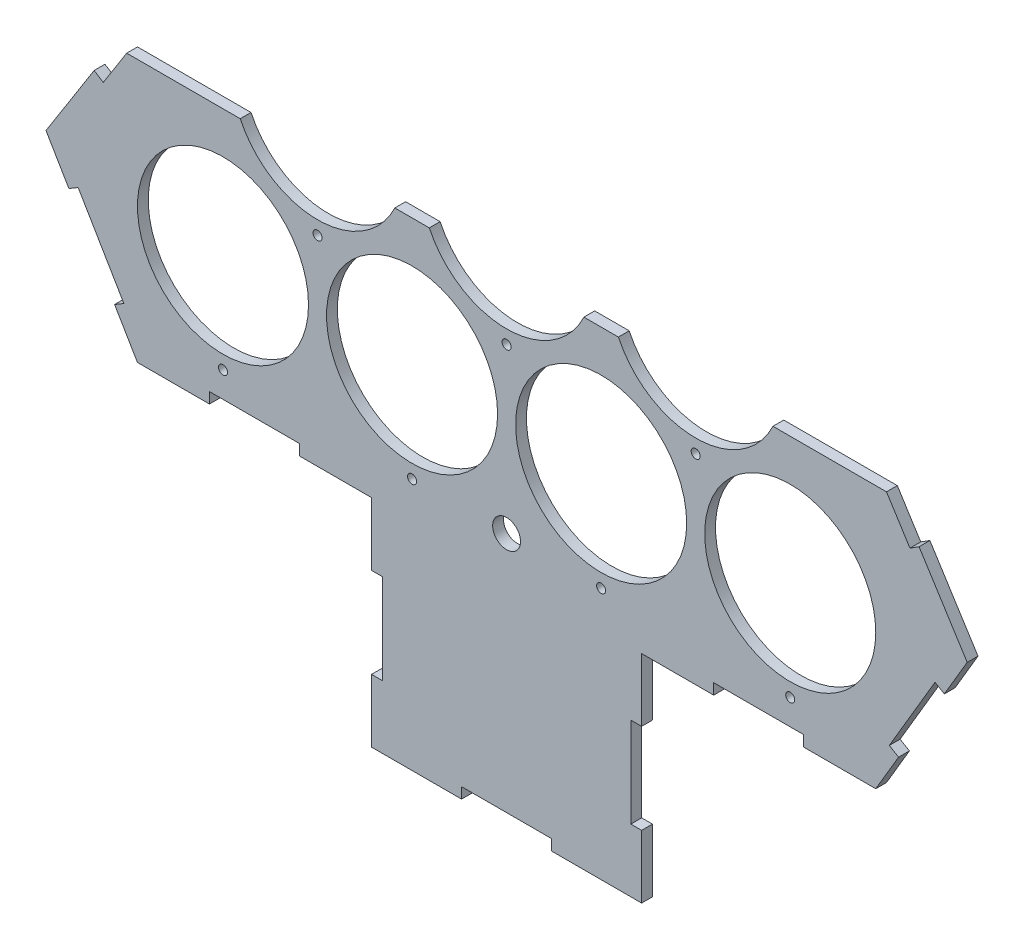
SolidWorks part; units mm, degrees
ref_plane "Plan de face" through (0, 0, 0) normal (0, 0, 1) x (1, 0, 0)
ref_plane "Plan de dessus" through (0, 0, 0) normal (0, 1, 0) x (1, 0, 0)
ref_plane "Plan de droite" through (0, 0, 0) normal (1, 0, 0) x (0, 0, -1)
sketch "Esquisse1" plane through (0, 0, 0) normal (0, 0, 1) x (1, 0, 0)
  line L0 (0, 0) -> (-371.1464, 0) construction
  line L1 (0, 0) -> (478.5179, 0) construction
  line L2 (0, 0) -> (0, 90.9327) construction
  line L3 (0, 90.9327) -> (-157.5, 90.9327) construction
  line L4 (0, 90.9327) -> (157.5, 90.9327) construction
  line L5 (0, 90.9327) -> (0, 181.8653) construction
  line L6 (0, 181.8653) -> (-52.5, 181.8653) construction
  line L7 (0, 181.8653) -> (52.5, 181.8653) construction
  line L8 (0, 181.8653) -> (0, 363.4062) construction
  line L12 (-255.7759, 10.9597) -> (-205, -75.1903)
  line L13 (205, -75.1903) -> (255.7759, 10.9597)
  line L14 (-50, 336.3537) -> (50, 336.3537)
  line L15 (-205, -75.1903) -> (205, -75.1903)
  line L16 (255.7759, 10.9597) -> (50, 336.3537)
  line L17 (-50, 336.3537) -> (-255.7759, 10.9597)
  line L18 (-50, 336.3537) -> (-50, -75.1903) construction
  line L19 (50, 336.3537) -> (50, -75.1903) construction
  circle A0 centre (-157.5, 0) radius 47.5
  circle A1 centre (-52.5, 0) radius 47.5
  circle A2 centre (52.5, 0) radius 47.5
  circle A3 centre (157.5, 0) radius 47.5
  circle A4 centre (-105, 90.9327) radius 47.5
  circle A5 centre (0, 90.9327) radius 47.5
  circle A6 centre (105, 90.9327) radius 47.5
  circle A7 centre (-52.5, 181.8653) radius 47.5
  circle A8 centre (52.5, 181.8653) radius 47.5
  circle A9 centre (0, 272.798) radius 47.5
  dimension "D1" = 95
  dimension "D2" = 95
  dimension "D3" = 95
  dimension "D4" = 95
  dimension "D5" = 105
  dimension "D6" = 52.5
  dimension "D7" = 52.5
  dimension "D8" = 105
  dimension "D9" = 95
  dimension "D10" = 95
  dimension "D11" = 95
  dimension "D12" = 105
  dimension "D13" = 105
  dimension "D14" = 105
  dimension "D15" = 95
  dimension "D16" = 95
  dimension "D17" = 105
  dimension "D18" = 52.5
  dimension "D19" = 52.5
  dimension "D20" = 95
  dimension "D21" = 105
  dimension "D27" = 205
  dimension "D22" = 385
  dimension "D23" = 385
  dimension "D24" = 410
  dimension "D25" = 32.309
  dimension "D26" = 32.309
  dimension "D28" = 100
  dimension "D30" = 100
  dimension "D31" = 100
extrude "Boss.-Extru.1" add sketch "Esquisse1" along normal blind 6
sketch "Esquisse9" plane through (0, 0, 6) normal (0, 0, 1) x (1, 0, 0)
  line L0 (-205, -75.1903) -> (205, -75.1903) construction
  line L1 (-75, -75.1903) -> (75, -75.1903)
  line L2 (-75, -75.1903) -> (-75, -195.1903)
  line L3 (-75, -195.1903) -> (75, -195.1903)
  line L4 (75, -75.1903) -> (75, -195.1903)
  dimension "D1" = 150
  dimension "D2" = 120
  dimension "D3" = 75
extrude "Boss.-Extru.2" add sketch "Esquisse9" against normal blind 6
sketch "Esquisse10" plane through (0, 0, 6) normal (0, 0, 1) x (1, 0, 0)
  line L0 (-75, -75.1903) -> (-75, -195.1903) construction
  line L1 (-75, -110.1903) -> (-69, -110.1903)
  line L2 (-75, -110.1903) -> (-75, -160.1903)
  line L3 (-75, -160.1903) -> (-69, -160.1903)
  line L4 (-69, -110.1903) -> (-69, -160.1903)
  line L5 (-75, -195.1903) -> (75, -195.1903) construction
  line L6 (-25, -195.1903) -> (25, -195.1903)
  line L7 (-25, -195.1903) -> (-25, -189.1903)
  line L8 (-25, -189.1903) -> (25, -189.1903)
  line L9 (25, -195.1903) -> (25, -189.1903)
  line L10 (-205, -75.1903) -> (-75, -75.1903) construction
  line L11 (-115, -75.1903) -> (-165, -75.1903)
  line L12 (-115, -75.1903) -> (-115, -69.1903)
  line L13 (-115, -69.1903) -> (-165, -69.1903)
  line L14 (-165, -75.1903) -> (-165, -69.1903)
  line L15 (-217.694, -53.6528) -> (-212.525, -50.6062)
  line L16 (-255.7759, 10.9597) -> (-205, -75.1903) construction
  line L17 (-212.525, -50.6062) -> (-237.9129, -7.5313)
  line L18 (-237.9129, -7.5313) -> (-243.0819, -10.5778)
  line L19 (-243.0819, -10.5778) -> (-217.694, -53.6528)
  line L20 (-229.0517, 53.2187) -> (-223.9806, 50.0118)
  line L21 (-50, 336.3537) -> (-255.7759, 10.9597) construction
  line L22 (-223.9806, 50.0118) -> (-170.5324, 134.5297)
  line L23 (-170.5324, 134.5297) -> (-175.6034, 137.7366)
  line L24 (-175.6034, 137.7366) -> (-229.0517, 53.2187)
  line L25 (-130.1724, 209.5768) -> (-125.1013, 206.3699)
  line L26 (-125.1013, 206.3699) -> (-71.6531, 290.8879)
  line L27 (-71.6531, 290.8879) -> (-76.7241, 294.0948)
  line L28 (-76.7241, 294.0948) -> (-130.1724, 209.5768)
  line L29 (50, 336.3537) -> (-50, 336.3537) construction
  line L30 (-25, 336.3537) -> (25, 336.3537)
  line L31 (-25, 336.3537) -> (-25, 330.3537)
  line L32 (-25, 330.3537) -> (25, 330.3537)
  line L33 (25, 336.3537) -> (25, 330.3537)
  line L34 (0, 336.3537) -> (0, -195.1903) construction
  line L35 (71.6531, 290.8879) -> (76.7241, 294.0948)
  line L36 (125.1013, 206.3699) -> (71.6531, 290.8879)
  line L37 (130.1724, 209.5768) -> (125.1013, 206.3699)
  line L38 (76.7241, 294.0948) -> (130.1724, 209.5768)
  line L39 (170.5324, 134.5297) -> (175.6034, 137.7366)
  line L40 (223.9806, 50.0118) -> (170.5324, 134.5297)
  line L41 (229.0517, 53.2187) -> (223.9806, 50.0118)
  line L42 (175.6034, 137.7366) -> (229.0517, 53.2187)
  line L43 (237.9129, -7.5313) -> (243.0819, -10.5778)
  line L44 (212.525, -50.6062) -> (237.9129, -7.5313)
  line L45 (217.694, -53.6528) -> (212.525, -50.6062)
  line L46 (243.0819, -10.5778) -> (217.694, -53.6528)
  line L47 (115, -69.1903) -> (165, -69.1903)
  line L48 (165, -75.1903) -> (165, -69.1903)
  line L49 (115, -75.1903) -> (165, -75.1903)
  line L50 (115, -75.1903) -> (115, -69.1903)
  line L51 (75, -160.1903) -> (69, -160.1903)
  line L52 (69, -110.1903) -> (69, -160.1903)
  line L53 (75, -110.1903) -> (69, -110.1903)
  line L54 (75, -110.1903) -> (75, -160.1903)
  dimension "D1" = 50
  dimension "D2" = 6
  dimension "D3" = 25
  dimension "D4" = 50
  dimension "D5" = 6
  dimension "D6" = 6
  dimension "D7" = 6
  dimension "D8" = 50
  dimension "D9" = 100
  dimension "D10" = 6
  dimension "D11" = 6
  dimension "D12" = 100
  dimension "D13" = 50
  dimension "D14" = 6
  dimension "D15" = 25
  dimension "D16" = 50
  dimension "D17" = 50
  dimension "D18" = 25
  dimension "D19" = 40
  dimension "D20" = 50
  dimension "D21" = 35
extrude "Enlèv. mat.-Extru.1" cut sketch "Esquisse10" against normal blind 10
sketch "Esquisse12" plane through (0, 0, 6) normal (0, 0, 1) x (1, 0, 0)
  line L0 (-25, 336.3537) -> (-50, 336.3537) construction
  line L1 (-346.5928, 336.3537) -> (328.9455, 336.3537)
  line L2 (-346.5928, 336.3537) -> (-346.5928, 70.5817)
  line L3 (-346.5928, 70.5817) -> (328.9455, 70.5817)
  line L4 (328.9455, 336.3537) -> (328.9455, 70.5817)
  dimension "D1" = 265.772
  dimension "D2" = 0
extrude "Enlèv. mat.-Extru.3" cut sketch "Esquisse12" against normal blind 10
sketch "Esquisse13" plane through (0, 0, 6) normal (0, 0, 1) x (1, 0, 0)
  circle A0 centre (-157.5, -55) radius 2.5
  circle A1 centre (-157.5, 0) radius 47.5 construction
  circle A2 centre (-52.5, -55) radius 2.5
  circle A3 centre (52.5, -55) radius 2.5
  circle A4 centre (157.5, -55) radius 2.5
  circle A5 centre (-105, 35.9327) radius 2.5
  arc A6 (-147.9196, 70.5817) -> (-62.0804, 70.5817) centre (-105, 90.9327) ccw construction
  circle A7 centre (0, 35.9327) radius 2.5
  circle A8 centre (105, 35.9327) radius 2.5
  dimension "D1" = 5
  dimension "D2" = 55
  dimension "D3" = 4
  dimension "D4" = 5
  dimension "D5" = 55
  dimension "D6" = 3
extrude "Enlèv. mat.-Extru.4" cut sketch "Esquisse13" against normal blind 10
sketch "Esquisse14" plane through (0, 0, 6) normal (0, 0, 1) x (1, 0, 0)
  circle A0 centre (0, -55) radius 7.75
  dimension "D1" = 15.5
  dimension "D2" = 55
extrude "Enlèv. mat.-Extru.5" cut sketch "Esquisse14" against normal blind 10
